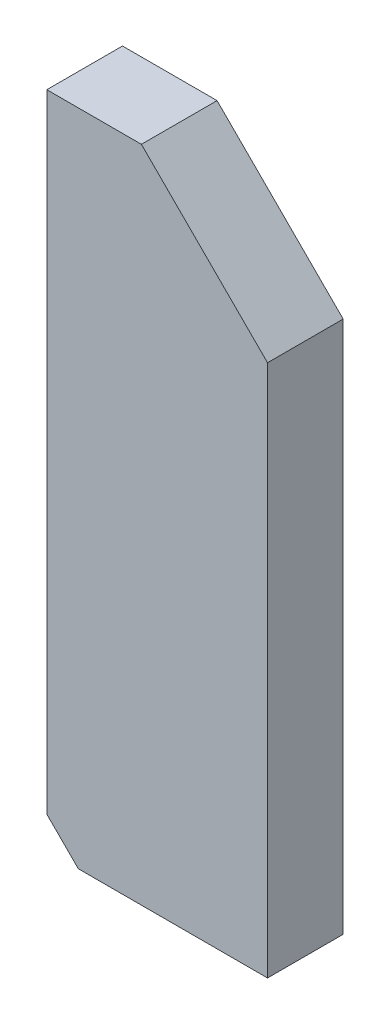
SolidWorks part; units mm, degrees
ref_plane "Front" through (0, 0, 0) normal (0, 0, 1) x (1, 0, 0)
ref_plane "Top" through (0, 0, 0) normal (0, 1, 0) x (1, 0, 0)
ref_plane "Right" through (0, 0, 0) normal (1, 0, 0) x (0, 0, -1)
sketch "Sketch1" plane through (0, 0, 0) normal (0, 0, 1) x (1, 0, 0)
  line L0 (15, 104.5) -> (35, 84.5)
  line L1 (5, 0) -> (35, 0)
  line L2 (0, 5) -> (0, 104.5)
  line L3 (0, 104.5) -> (15, 104.5)
  line L4 (35, 0) -> (35, 84.5)
  line L5 (0, 5) -> (5, 0)
  dimension "D1" = 5
  dimension "D2" = 5
  dimension "D3" = 104.5
  dimension "D4" = 35
  dimension "D5" = 84.5
  dimension "D6" = 15
extrude "Boss-Extrude1" add sketch "Sketch1" along normal blind 12
hole_wizard "M5x0.8 Tapped Hole1" positions "Sketch3" profile "Sketch2" tap size "M5x0.8" standard "JIS"
sketch "Sketch3" plane through (0, 0, 0) normal (-1, 0, 0) x (0, 0, 1)
  line L1 (0, 104.5) -> (0, 5) construction
  line L2 (12, 0) -> (0, 0) construction
  point P0 (6, 90)
  point P1 (6, 20)
  dimension "D1" = 6
  dimension "D2" = 20
  dimension "D3" = 70
sketch "Sketch2" plane through (0, 90, 6) normal (0, 1, 0) x (0, 0, 1)
  line L0 (0, 0) -> (0, 17.2618)
  line L1 (0, 17.2618) -> (2.1, 16)
  line L2 (2.1, 16) -> (2.1, 0)
  line L5 (2.1, 0) -> (0, 0)
  line L10 (0, 17.2618) -> (-2.1, 16) construction
  line L11 (0, -6.35) -> (0, 107.95) construction
  dimension "ねじ下穴ﾄﾞﾘﾙ直径" = 4.2
  dimension "ねじ下穴ﾄﾞﾘﾙの深さ" = 16
  dimension "ﾄﾞﾘﾙ角度" = 118
cosmetic thread "Hole Thread1"
cosmetic thread "Hole Thread2"
hole_wizard "M5x0.8 Tapped Hole2" positions "Sketch5" profile "Sketch4" tap size "M5x0.8" standard "JIS"
sketch "Sketch5" plane through (0, 0, 0) normal (0, -1, 0) x (1, 0, 0)
  point P0 (25, 6)
  dimension "D1" = 6
  dimension "D2" = 25
sketch "Sketch4" plane through (25, 0, 6) normal (1, 0, 0) x (0, 0, -1)
  line L0 (0, 0) -> (0, 15.2618)
  line L1 (0, 15.2618) -> (2.1, 14)
  line L2 (2.1, 14) -> (2.1, 0)
  line L5 (2.1, 0) -> (0, 0)
  line L10 (0, 15.2618) -> (-2.1, 14) construction
  line L11 (0, -6.35) -> (0, 107.95) construction
  dimension "ねじ下穴ﾄﾞﾘﾙ直径" = 4.2
  dimension "ねじ下穴ﾄﾞﾘﾙの深さ" = 14
  dimension "ﾄﾞﾘﾙ角度" = 118
cosmetic thread "Hole Thread3"
